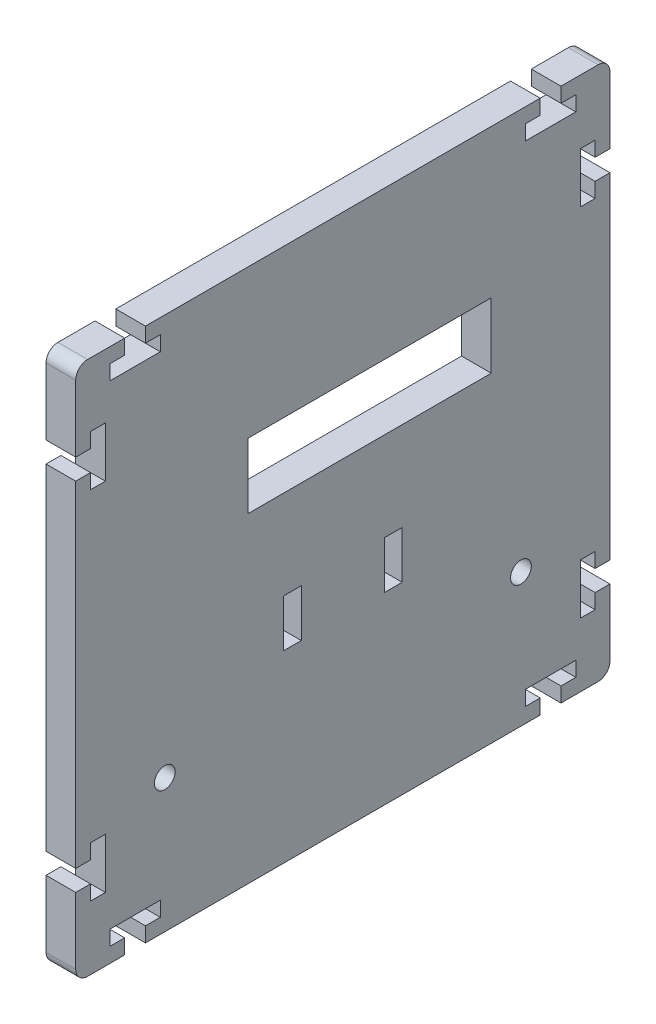
SolidWorks part; units mm, degrees
ref_plane "Спереди" through (0, 0, 0) normal (0, 0, 1) x (1, 0, 0)
ref_plane "Сверху" through (0, 0, 0) normal (0, 1, 0) x (1, 0, 0)
ref_plane "Справа" through (0, 0, 0) normal (1, 0, 0) x (0, 0, -1)
sketch "Эскиз1" plane through (0, 0, 0) normal (1, 0, 0) x (0, 0, -1)
  line L0 (-36.75, 45) -> (-36.75, 42.5)
  line L1 (-43, -45) -> (-36.75, -45)
  line L2 (-45, -43) -> (-45, -31.75)
  line L3 (-43, 45) -> (-36.75, 45)
  line L4 (45, -43) -> (45, -31.75)
  line L5 (-45, -45) -> (45, 45) construction
  line L6 (-45, 45) -> (45, -45) construction
  line L7 (-36.75, 42.5) -> (-39.25, 42.5)
  line L8 (-39.25, 42.5) -> (-39.25, 40)
  line L9 (-39.25, 40) -> (-30.75, 40)
  line L10 (-33.25, 45) -> (33.25, 45)
  line L11 (-30.75, 42.5) -> (-30.75, 40)
  line L12 (-33.25, 42.5) -> (-30.75, 42.5)
  line L13 (-33.25, 45) -> (-33.25, 42.5)
  line L14 (0, 0) -> (0, 21.2721) construction
  line L15 (0, 0) -> (18.8007, 0) construction
  line L16 (33.25, 45) -> (33.25, 42.5)
  line L17 (33.25, 42.5) -> (30.75, 42.5)
  line L18 (30.75, 42.5) -> (30.75, 40)
  line L19 (39.25, 40) -> (30.75, 40)
  line L20 (39.25, 42.5) -> (39.25, 40)
  line L21 (36.75, 42.5) -> (39.25, 42.5)
  line L22 (36.75, 45) -> (36.75, 42.5)
  line L23 (-33.25, -45) -> (-33.25, -42.5)
  line L24 (-33.25, -42.5) -> (-30.75, -42.5)
  line L25 (-30.75, -42.5) -> (-30.75, -40)
  line L26 (-39.25, -40) -> (-30.75, -40)
  line L27 (-39.25, -42.5) -> (-39.25, -40)
  line L28 (-36.75, -42.5) -> (-39.25, -42.5)
  line L29 (-36.75, -45) -> (-36.75, -42.5)
  line L30 (36.75, -45) -> (36.75, -42.5)
  line L31 (36.75, -42.5) -> (39.25, -42.5)
  line L32 (39.25, -42.5) -> (39.25, -40)
  line L33 (39.25, -40) -> (30.75, -40)
  line L34 (30.75, -42.5) -> (30.75, -40)
  line L35 (33.25, -42.5) -> (30.75, -42.5)
  line L36 (33.25, -45) -> (33.25, -42.5)
  line L37 (36.75, 45) -> (43, 45)
  line L38 (36.75, -45) -> (43, -45)
  line L39 (-33.25, -45) -> (33.25, -45)
  line L40 (-42.5, 28.25) -> (-42.5, 25.75)
  line L41 (-42.5, 34.25) -> (-40, 34.25)
  line L42 (-42.5, 34.25) -> (-42.5, 31.75)
  line L43 (-42.5, 25.75) -> (-40, 25.75)
  line L44 (-40, 34.25) -> (-40, 25.75)
  line L45 (-42.5, 31.75) -> (-45, 31.75)
  line L46 (-50, -45) -> (50, 45) construction
  line L47 (-42.5, 28.25) -> (-45, 28.25)
  line L48 (-50, 45) -> (50, -45) construction
  line L49 (-45, 31.75) -> (-45, 43)
  line L50 (0, 0) -> (0, 21.2721) construction
  line L51 (-13, -23) -> (13, 3) construction
  line L52 (13, 3) -> (13, -23) construction
  line L53 (13, -23) -> (-13, -23) construction
  line L54 (-13, 3) -> (-13, -23) construction
  line L55 (13, -23) -> (-13, 3) construction
  line L56 (0, -10) -> (0, -23) construction
  line L57 (0, -10) -> (-8.5, -10) construction
  line L58 (10, -6) -> (7, -6)
  line L59 (-10, -14) -> (-7, -14)
  line L60 (-10, -14) -> (-10, -6)
  line L61 (-10, -6) -> (-7, -6)
  line L62 (-42.5, -28.25) -> (-45, -28.25)
  line L63 (-42.5, -31.75) -> (-45, -31.75)
  line L64 (-40, -34.25) -> (-40, -25.75)
  line L65 (-42.5, -25.75) -> (-40, -25.75)
  line L66 (-42.5, -34.25) -> (-42.5, -31.75)
  line L67 (-42.5, -34.25) -> (-40, -34.25)
  line L68 (-42.5, -28.25) -> (-42.5, -25.75)
  line L69 (42.5, -28.25) -> (42.5, -25.75)
  line L70 (42.5, -34.25) -> (40, -34.25)
  line L71 (42.5, -34.25) -> (42.5, -31.75)
  line L72 (42.5, -25.75) -> (40, -25.75)
  line L73 (40, -34.25) -> (40, -25.75)
  line L74 (42.5, -31.75) -> (45, -31.75)
  line L75 (42.5, -28.25) -> (45, -28.25)
  line L76 (42.5, 28.25) -> (45, 28.25)
  line L77 (42.5, 31.75) -> (45, 31.75)
  line L78 (40, 34.25) -> (40, 25.75)
  line L79 (42.5, 25.75) -> (40, 25.75)
  line L80 (42.5, 34.25) -> (42.5, 31.75)
  line L81 (42.5, 34.25) -> (40, 34.25)
  line L82 (42.5, 28.25) -> (42.5, 25.75)
  line L83 (-45, -28.25) -> (-45, 28.25)
  line L84 (45, -28.25) -> (45, 28.25)
  line L85 (45, 31.75) -> (45, 43)
  line L86 (-7, -14) -> (-7, -6)
  line L87 (-10, -14) -> (-7, -6) construction
  line L88 (-10, -6) -> (-7, -14) construction
  line L89 (10, -14) -> (7, -14)
  line L90 (10, -14) -> (10, -6)
  line L91 (7, -14) -> (7, -6)
  line L93 (25, 9) -> (-16, 9)
  line L94 (25, 9) -> (25, 20)
  line L95 (25, 20) -> (-16, 20)
  line L96 (-16, 9) -> (-16, 20)
  line L97 (25, 9) -> (-16, 20) construction
  line L98 (25, 20) -> (-16, 9) construction
  arc A0 (43, 45) -> (45, 43) centre (43, 43) cw
  arc A1 (45, -43) -> (43, -45) centre (43, -43) cw
  arc A2 (-45, -43) -> (-43, -45) centre (-43, -43) ccw
  arc A3 (-43, 45) -> (-45, 43) centre (-43, 43) ccw
  circle A4 centre (-30, -22.5) radius 1.75
  circle A5 centre (30, -22.5) radius 1.75
  point P0 (0, 0)
  point P16 (-37, 42.5)
  point P27 (37, 42.5)
  point P36 (-37, -42.5)
  point P45 (37, -42.5)
  point P115 (4.5, 14.5)
  dimension "D10" = 13.25
  dimension "D16" = 2
  dimension "D17" = 2
  dimension "D23" = 3.5
  dimension "D1" = 90
  dimension "D2" = 90
  dimension "D3" = 3.5
  dimension "D4" = 8.25
  dimension "D5" = 2.5
  dimension "D6" = 2.5
  dimension "D7" = 5
  dimension "D8" = 2.5
  dimension "D9" = 8.5
  dimension "D11" = 3.5
  dimension "D12" = 2.5
  dimension "D13" = 8.5
  dimension "D14" = 2.5
  dimension "D15" = 2.5
  dimension "D18" = 55
  dimension "D19" = 90
  dimension "D20" = 8.5
  dimension "D21" = 3
  dimension "D22" = 8
  dimension "D24" = 15
  dimension "D25" = 67.5
  dimension "D26" = 15
  dimension "D27" = 20
  dimension "D28" = 41
  dimension "D29" = 11
  dimension "D30" = 25
extrude "Бобышка-Вытянуть1" add sketch "Эскиз1" along normal blind 5
